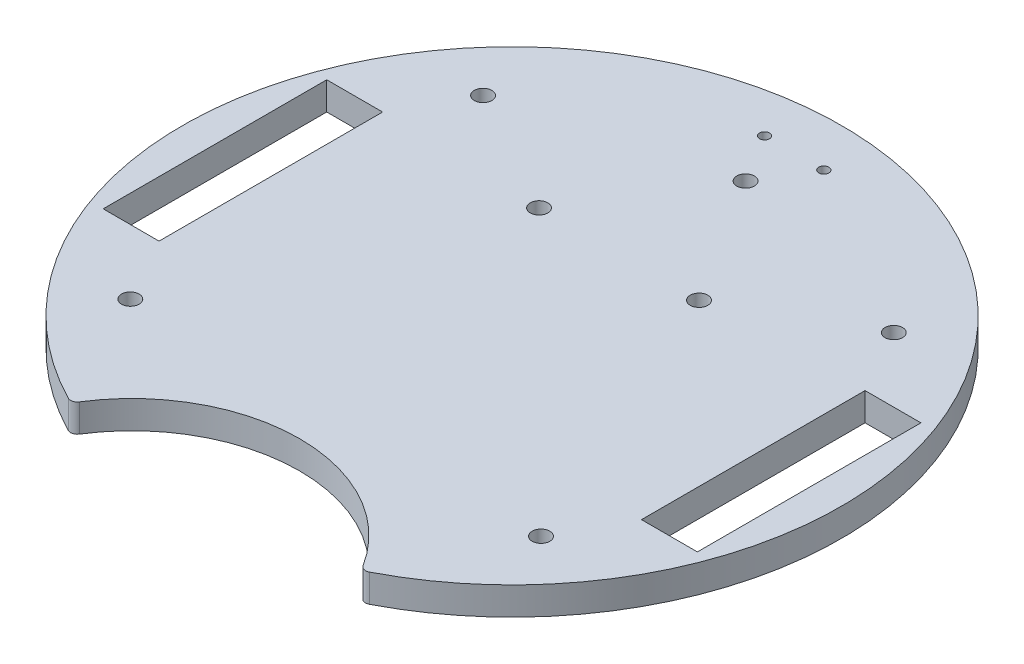
SolidWorks part; units mm, degrees
ref_plane "Front Plane" through (0, 0, 0) normal (0, 0, 1) x (1, 0, 0)
ref_plane "Top Plane" through (0, 0, 0) normal (0, 1, 0) x (1, 0, 0)
ref_plane "Right Plane" through (0, 0, 0) normal (1, 0, 0) x (0, 0, -1)
sketch "Sketch1" plane through (0, 0, 0) normal (0, 1, 0) x (1, 0, 0)
  line L3 (-32.9956, -67.352) -> (0, -86.402) construction
  line L4 (32.9956, -67.352) -> (0, -86.402) construction
  line L9 (54.8141, -25.4) -> (54.8141, 25.4)
  line L10 (-67.5141, -25.4) -> (-54.8141, -25.4)
  line L11 (-67.5141, -25.4) -> (-67.5141, 25.4)
  line L12 (-67.5141, 25.4) -> (-54.8141, 25.4)
  line L13 (-54.8141, 25.4) -> (-54.8141, -25.4)
  line L14 (67.5141, 25.4) -> (54.8141, 25.4)
  line L15 (67.5141, -25.4) -> (67.5141, 25.4)
  line L16 (67.5141, -25.4) -> (54.8141, -25.4)
  arc A1 (32.2407, -66.1006) -> (-32.2407, -66.1006) centre (0, -86.402) ccw
  arc A2 (34.1948, -66.6358) -> (-34.1948, -66.6358) centre (0, 0) ccw
  circle A25 centre (-18.179, 24.3106) radius 2
  circle A38 centre (-46.6637, -40.0812) radius 2
  circle A39 centre (46.6637, -40.0812) radius 2
  circle A40 centre (46.6637, 40.0812) radius 2
  circle A41 centre (-46.6637, 40.0812) radius 2
  arc A42 (-34.1948, -66.6358) -> (-32.2407, -66.1006) centre (-33.51, -65.3013) ccw
  arc A43 (34.1948, -66.6358) -> (32.2407, -66.1006) centre (33.51, -65.3013) cw
  circle A44 centre (-6.731, 64.1077) radius 1.143
  circle A45 centre (6.731, 64.1077) radius 1.143
  circle A47 centre (18.179, 24.3106) radius 2
  circle A48 centre (0, 53.0612) radius 2
  dimension "D3" = 120
  dimension "D18" = 2.286
  dimension "D12" = 4
  dimension "D4" = 50.8
  dimension "D5" = 12.7
extrude "Boss-Extrude3" add sketch "Sketch1" along normal blind 6.35
